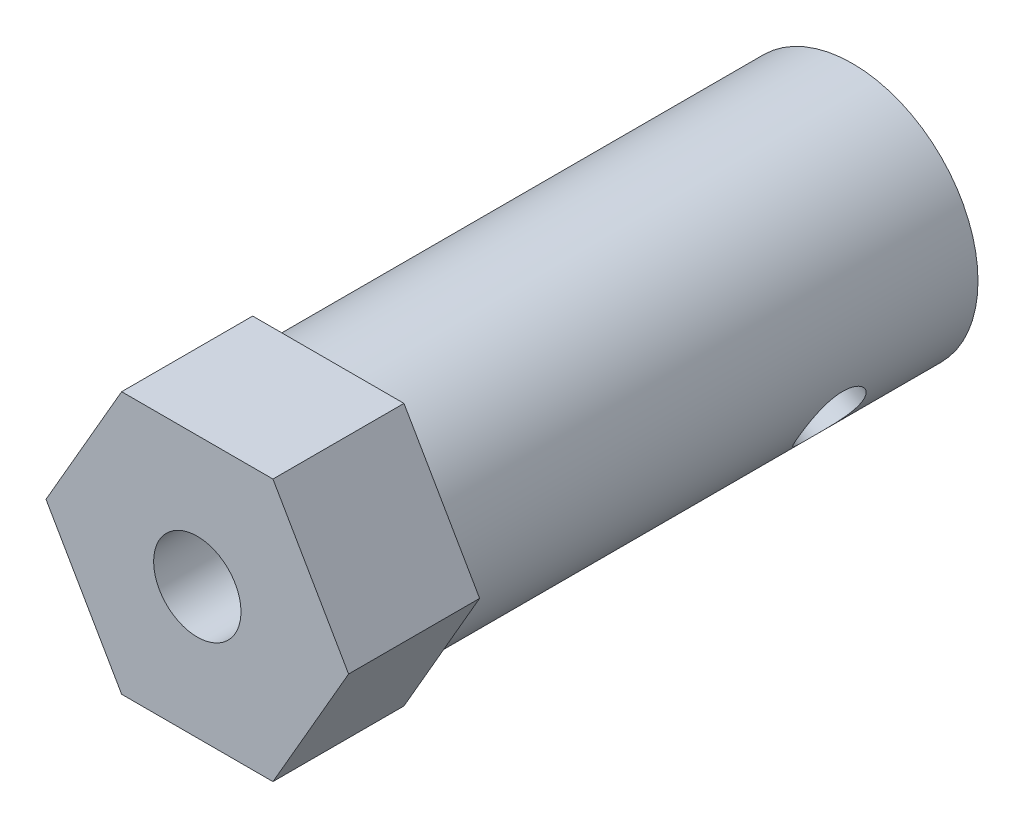
SolidWorks part; units mm, degrees
material "Brass"
ref_plane "Front Plane" through (0, 0, 0) normal (1, 0, 0) x (0, 1, 0)
ref_plane "Top Plane" through (0, 0, 0) normal (0, 0, 1) x (0, 1, 0)
ref_plane "Right Plane" through (0, 0, 0) normal (0, 1, 0) x (-1, 0, 0)
sketch "Sketch1" plane through (0, 0, 0) normal (0, 0, 1) x (0, 1, 0)
  line L1 (0, 6.9282) -> (-6, 3.4641)
  line L2 (-6, 3.4641) -> (-6, -3.4641)
  line L3 (-6, -3.4641) -> (0, -6.9282)
  line L4 (0, -6.9282) -> (6, -3.4641)
  line L5 (6, -3.4641) -> (6, 3.4641)
  line L6 (6, 3.4641) -> (0, 6.9282)
  circle A0 centre (0, 0) radius 6 construction
  dimension "D1" = 12
extrude "Boss-Extrude1" add sketch "Sketch1" along normal blind 6
sketch "Sketch2" plane through (0, 0, 0) normal (0, 0, -1) x (1, 0, 0)
  circle A0 centre (0, 0) radius 5.75
  dimension "D1" = 11.5
extrude "Boss-Extrude2" add sketch "Sketch2" along normal blind 24
sketch "Sketch4" plane through (0, 0, -24) normal (0, 0, -1) x (1, 0, 0)
  circle A0 centre (0, 0) radius 2
  dimension "D1" = 4
extrude "Cut-Extrude2" cut sketch "Sketch4" against normal through all
ref_plane "Plane1" through (5.1962, -3, 0) normal (0.866, -0.5, 0) x (0, 0, -1)
sketch "Sketch5" plane through (5.1962, -3, 0) normal (0.866, -0.5, 0) x (0.5, 0.866, 0)
  line L0 (-3.4641, 0) -> (3.4641, 0) construction
  circle A0 centre (0, -18) radius 1.5
  dimension "D2" = 3
  dimension "D1" = 18
extrude "Cut-Extrude3" cut sketch "Sketch5" against normal blind 6 contours A0
